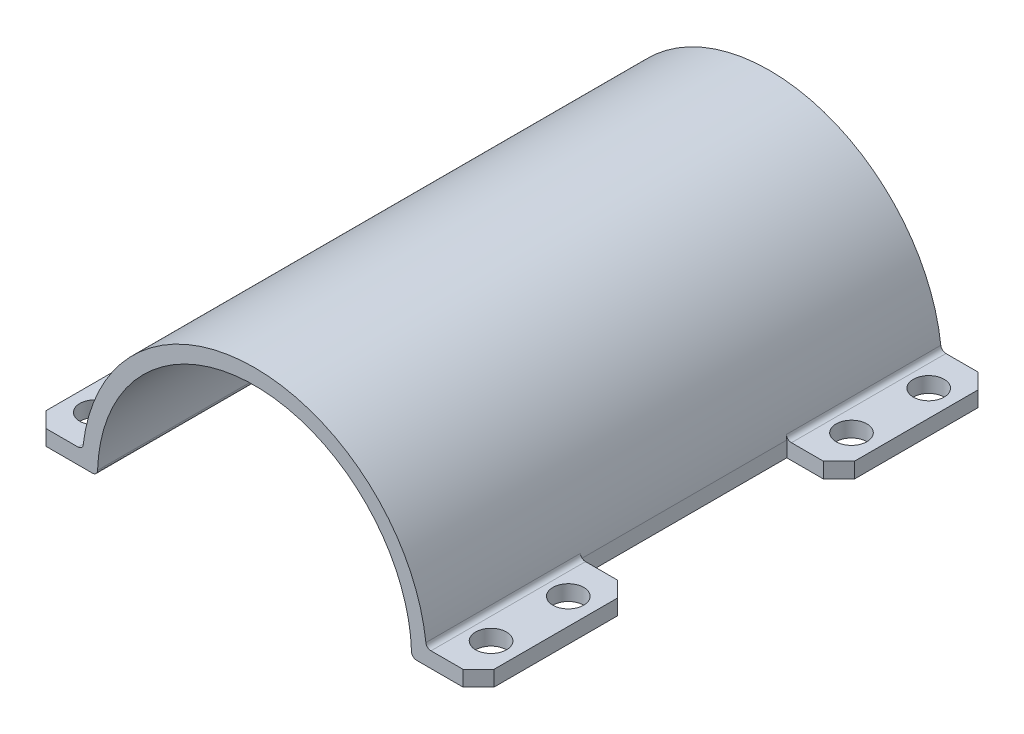
SolidWorks part; units mm, degrees
material "1060 Alloy"
ref_plane "Front Plane" through (0, 0, 0) normal (0, 0, 1) x (1, 0, 0)
ref_plane "Top Plane" through (0, 0, 0) normal (0, 1, 0) x (1, 0, 0)
ref_plane "Right Plane" through (0, 0, 0) normal (1, 0, 0) x (0, 0, -1)
sketch "Sketch1" plane through (0, 0, 0) normal (0, 0, 1) x (1, 0, 0)
  line L0 (0, 0) -> (-30.5, 0) construction
  line L1 (-30.5, 0) -> (-33.5, 0)
  line L2 (0, 0) -> (30.5, 0) construction
  line L3 (30.5, 0) -> (33.5, 0)
  line L4 (33.5, 0) -> (43.5, 0)
  line L5 (43.5, 0) -> (43.5, 3)
  line L6 (43.5, 3) -> (33.3654, 3)
  line L7 (-33.5, 0) -> (-43.5, 0)
  line L8 (-43.5, 0) -> (-43.5, 3)
  line L9 (-43.5, 3) -> (-33.3654, 3)
  circle A0 centre (0, 0) radius 30 construction
  circle A1 centre (0, 0) radius 30.5
  circle A2 centre (0, 0) radius 33.5
  dimension "D1" = 60
  dimension "D2" = 0.5
  dimension "D3" = 3
  dimension "D4" = 3
  dimension "D5" = 3
  dimension "D6" = 10
  dimension "D7" = 10
extrude "Boss-Extrude1" add sketch "Sketch1" along normal blind 100 contours A2 L9 L8 L7 | L3 A2 L1 A1 | A2 L4 L5 L6
sketch "Sketch3" plane through (0, 3, 0) normal (0, 1, 0) x (1, 0, 0)
  line L0 (43.5, -100) -> (43.5, 0) construction
  line L1 (43.5, -30) -> (33.3654, -30)
  line L2 (43.5, -30) -> (43.5, -70)
  line L3 (43.5, -70) -> (33.3654, -70)
  line L4 (33.3654, -30) -> (33.3654, -70)
  line L5 (33.3654, -100) -> (33.3654, 0) construction
  line L6 (-43.5, -100) -> (-43.5, 0) construction
  line L7 (-43.5, -30) -> (-33.3654, -30)
  line L8 (-43.5, -30) -> (-43.5, -70)
  line L9 (-43.5, -70) -> (-33.3654, -70)
  line L10 (-33.3654, -30) -> (-33.3654, -70)
  line L11 (-33.3654, -100) -> (-33.3654, 0) construction
  line L12 (-43.5, 0) -> (-33.3654, 0) construction
  line L13 (43.5, 0) -> (33.3654, 0) construction
  line L14 (43.5, -100) -> (33.3654, -100) construction
  line L15 (-43.5, -100) -> (-33.3654, -100) construction
  dimension "D1" = 30
  dimension "D2" = 30
  dimension "D3" = 30
  dimension "D4" = 30
extrude "Cut-Extrude1" cut sketch "Sketch3" against normal blind 60
sketch "Sketch4" plane through (0, 3, 0) normal (0, 1, 0) x (1, 0, 0)
  line L0 (38.4327, -30) -> (38.4327, 0) construction
  line L1 (43.5, -30) -> (33.3654, -30) construction
  line L2 (43.5, 0) -> (33.3654, 0) construction
  circle A0 centre (38.4327, -22.5) radius 3
  circle A1 centre (38.4327, -7.5) radius 3
  dimension "D1" = 6
  dimension "D2" = 6
  dimension "D3" = 7.5
  dimension "D4" = 7.5
extrude "Cut-Extrude2" cut sketch "Sketch4" against normal blind 60
ref_plane "Plane1" through (0, 0, 0) normal (1, 0, 0) x (0, 0, -1)
ref_plane "Plane2" through (0, 0, 50) normal (0, 0, -1) x (-1, 0, 0)
mirror "Mirror3" about plane through (0, 0, 50) normal (0, 0, -1) of "Cut-Extrude2"
mirror "Mirror4" about plane through (0, 0, 0) normal (1, 0, 0) of "Mirror3", "Cut-Extrude2"
chamfer "Chamfer1" distance 3 angle 45 8 edges at (43.5, 1.5, 30) (43.5, 1.5, 0) (43.5, 1.5, 70) (43.5, 1.5, 100) (-43.5, 1.5, 30) (-43.5, 1.5, 70) (-43.5, 1.5, 100) (-43.5, 1.5, 0)
fillet "Fillet1" radius 1 6 edges at (-33.3654, 3, 85) (-33.3654, 3, 15) (33.3654, 3, 85) (33.3654, 3, 15) (-30.5, 0, 50) (30.5, 0, 50)
equation "\"D3@Sketch4\"=7.5"
